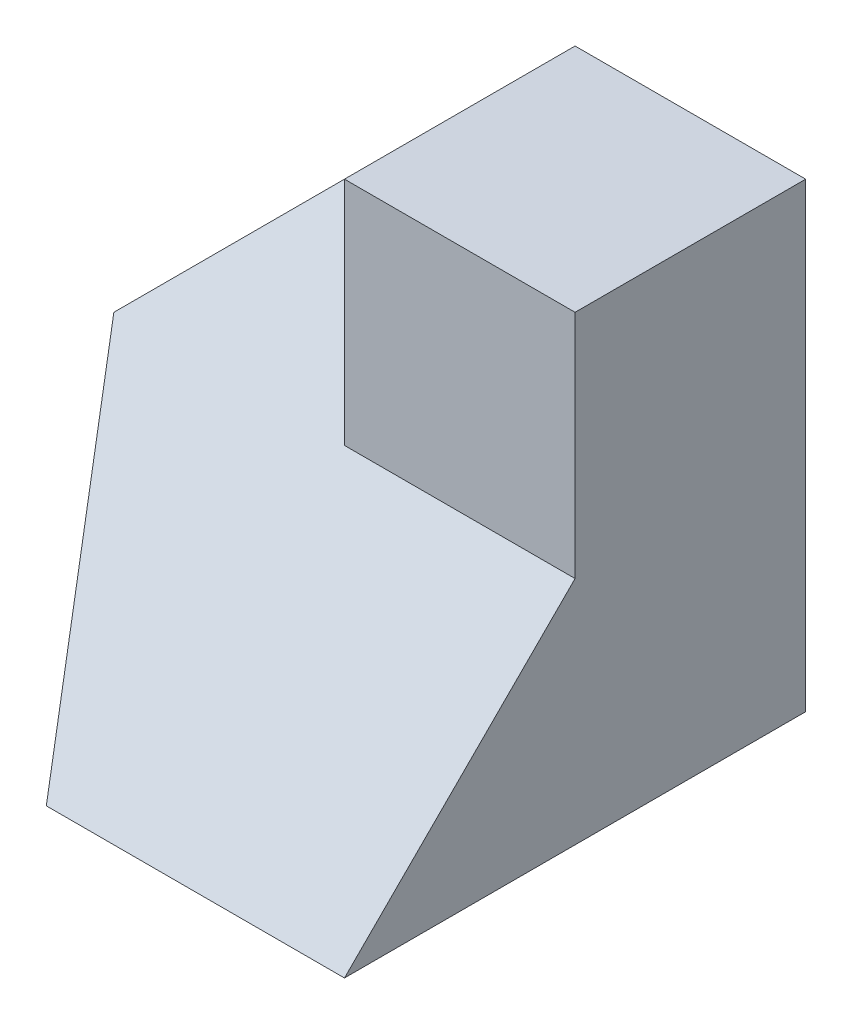
SolidWorks part; units mm, degrees
ref_plane "Front Plane" through (0, 0, 0) normal (0, 0, 1) x (1, 0, 0)
ref_plane "Top Plane" through (0, 0, 0) normal (0, 1, 0) x (1, 0, 0)
ref_plane "Right Plane" through (0, 0, 0) normal (1, 0, 0) x (0, 0, -1)
sketch "Sketch1" plane through (0, 0, 0) normal (0, 0, 1) x (1, 0, 0)
  line L1 (0, 0) -> (40, 0)
  line L2 (0, 0) -> (0, 40)
  line L3 (0, 40) -> (40, 40)
  line L4 (40, 0) -> (40, 40)
  dimension "D1" = 40
  dimension "D2" = 40
extrude "Boss-Extrude1" add sketch "Sketch1" along normal blind 40
sketch "Sketch2" plane through (0, 0, 40) normal (0, 0, 1) x (1, 0, 0)
  line L0 (0, 20) -> (0, 40)
  line L1 (0, 40) -> (0, 0) construction
  line L2 (0, 40) -> (20, 40)
  line L3 (40, 40) -> (0, 40) construction
  line L4 (20, 40) -> (0, 20)
extrude "Cut-Extrude1" cut sketch "Sketch2" against normal blind 40
sketch "Sketch3" plane through (0, 0, 0) normal (-1, 0, 0) x (0, 0, 1)
  line L0 (40, 0) -> (20, 20)
  line L1 (0, 20) -> (40, 20) construction
  line L2 (20, 20) -> (0, 40)
  line L3 (0, 40) -> (40, 40)
  line L4 (40, 40) -> (40, 0)
  line L6 (40, 20) -> (40, 0) construction
  point P5 (40, 20)
  point P8 (40, 20)
  point P10 (40, 20)
  point P12 (0, 0)
  point P14 (40, -0.5963)
  dimension "D1" = 40
  dimension "D2" = 20
  dimension "D3" = 180
extrude "Cut-Extrude2" cut sketch "Sketch3" against normal blind 40
sketch "Sketch4" plane through (0, 20, 20) normal (0, 0.7071, 0.7071) x (1, 0, 0)
  line L0 (0, 0) -> (20, -40)
  line L2 (20, -40) -> (0, -40)
  line L3 (0, -40) -> (0, 0)
  point P5 (0, 0)
extrude "Cut-Extrude3" cut sketch "Sketch4" against normal blind 40
sketch "Sketch5" plane through (40, 0, 0) normal (1, 0, 0) x (0, 0, -1)
  line L0 (-40, 0) -> (0, 0) construction
  line L1 (0, 40) -> (-20, 40)
  line L2 (0, 40) -> (0, 0)
  line L3 (0, 0) -> (-20, 0)
  line L4 (-20, 40) -> (-20, 0)
extrude "Boss-Extrude2" add sketch "Sketch5" against normal blind 20
